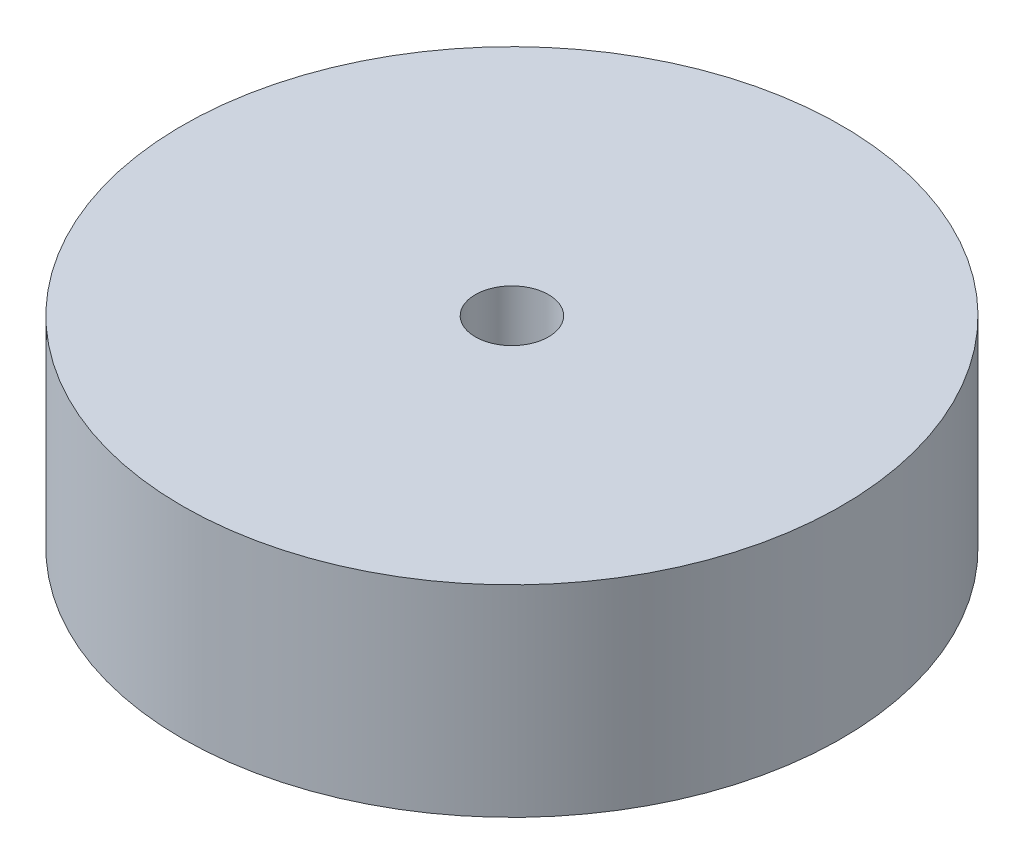
SolidWorks part; units mm, degrees
ref_plane "Front Plane" through (0, 0, 0) normal (0, 0, 1) x (1, 0, 0)
ref_plane "Top Plane" through (0, 0, 0) normal (0, 1, 0) x (1, 0, 0)
ref_plane "Right Plane" through (0, 0, 0) normal (1, 0, 0) x (0, 0, -1)
sketch "Sketch1" plane through (0, 0, 0) normal (0, 1, 0) x (1, 0, 0)
  line L1 (4.7631, -2.75) -> (0, 5.5) construction
  line L2 (0, 5.5) -> (-4.7631, -2.75) construction
  line L3 (-4.7631, -2.75) -> (4.7631, -2.75) construction
  circle A0 centre (0, 0) radius 5.5 construction
  circle A1 centre (-4.7631, -2.75) radius 2
  circle A2 centre (0, 5.5) radius 2
  circle A3 centre (4.7631, -2.75) radius 2
  circle A4 centre (0, 0) radius 9
  circle A5 centre (0, 0) radius 2.25
  dimension "D2" = 4
  dimension "D3" = 18
  dimension "D4" = 4.5
  dimension "D1" = 5.5
extrude "Boss-Extrude1" add sketch "Sketch1" along normal blind 2.5
sketch "Sketch2" plane through (0, 2.5, 0) normal (0, 1, 0) x (1, 0, 0)
  circle A0 centre (0, 0) radius 9
  dimension "D1" = 18
extrude "Boss-Extrude2" add sketch "Sketch2" along normal blind 3
sketch "Sketch3" plane through (0, 5.5, 0) normal (0, 1, 0) x (1, 0, 0)
  circle A0 centre (0, 0) radius 1
  dimension "D1" = 2
extrude "Cut-Extrude1" cut sketch "Sketch3" against normal through all
